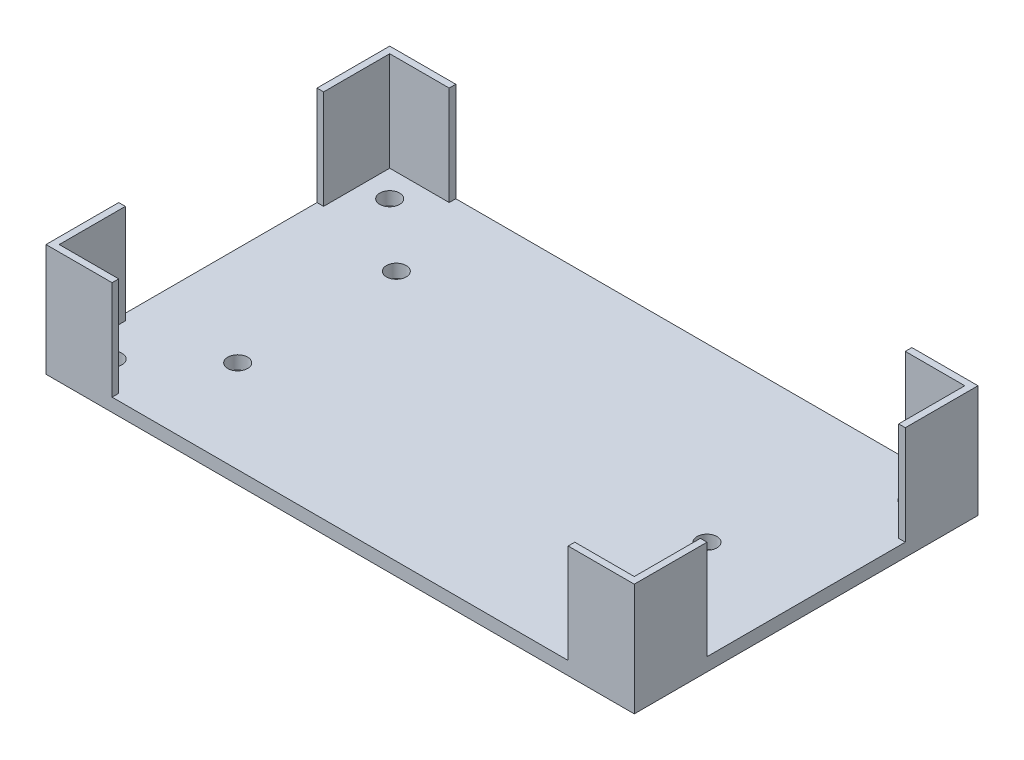
SolidWorks part; units mm, degrees
ref_plane "Front Plane" through (0, 0, 0) normal (0, 0, 1) x (1, 0, 0)
ref_plane "Top Plane" through (0, 0, 0) normal (0, 1, 0) x (1, 0, 0)
ref_plane "Right Plane" through (0, 0, 0) normal (1, 0, 0) x (0, 0, -1)
sketch "Sketch1" plane through (0, 0, 0) normal (0, 1, 0) x (1, 0, 0)
  line L1 (-60.2291, 12.7329) -> (28.7709, 12.7329)
  line L2 (-60.2291, 12.7329) -> (-60.2291, -39.2671)
  line L3 (-60.2291, -39.2671) -> (28.7709, -39.2671)
  line L4 (28.7709, 12.7329) -> (28.7709, -39.2671)
  dimension "D1" = 52
  dimension "D2" = 89
extrude "Boss-Extrude1" add sketch "Sketch1" along normal blind 2 contours L2 L1 L4 L3
sketch "Sketch2" plane through (0, 2, 0) normal (0, 1, 0) x (1, 0, 0)
  line L0 (-60.2291, 12.7329) -> (-60.2291, -39.2671) construction
  line L1 (-60.2291, -39.2671) -> (28.7709, -39.2671) construction
  line L2 (-60.2291, 12.7329) -> (28.7709, 12.7329) construction
  line L3 (28.7709, 12.7329) -> (28.7709, -39.2671) construction
  circle A0 centre (-55.2291, -34.2671) radius 1.5
  circle A1 centre (-55.2291, 7.7329) radius 1.5
  circle A2 centre (23.7709, 7.7329) radius 1.5
  circle A3 centre (23.7709, -34.2671) radius 1.5
  point P16 (0, 0)
  point P17 (0, 0)
  point P18 (0, 0)
  dimension "D1" = 3
  dimension "D4" = 3
  dimension "D7" = 3
  dimension "D8" = 5
  dimension "D12" = 3
  dimension "D2" = 5
  dimension "D3" = 5
  dimension "D5" = 5
  dimension "D6" = 5
  dimension "D9" = 5
  dimension "D10" = 5
  dimension "D11" = 5
extrude "Cut-Extrude1" cut sketch "Sketch2" against normal through all
sketch "Sketch5" plane through (0, 2, 0) normal (0, 1, 0) x (1, 0, 0)
  line L0 (-60.2291, 12.7329) -> (-60.2291, -39.2671) construction
  line L1 (-60.2291, -39.2671) -> (28.7709, -39.2671) construction
  line L3 (28.7709, 12.7329) -> (28.7709, -39.2671) construction
  circle A0 centre (-45.2291, -25.2671) radius 1.5
  circle A1 centre (-45.2291, -1.2671) radius 1.5
  circle A2 centre (13.7709, -13.2671) radius 1.5
  point P10 (0, 0)
  point P11 (0, 0)
  dimension "D1" = 3
  dimension "D2" = 3
  dimension "D3" = 3
  dimension "D4" = 15
  dimension "D5" = 14
  dimension "D6" = 15
  dimension "D7" = 24
  dimension "D8" = 26
  dimension "D9" = 15
extrude "Cut-Extrude3" cut sketch "Sketch5" against normal through all
sketch "Sketch6" plane through (0, 2, 0) normal (0, 1, 0) x (1, 0, 0)
  line L0 (-60.2291, 12.7329) -> (-60.2291, -39.2671) construction
  line L1 (-60.2291, -38.2671) -> (-59.2291, -38.2671)
  line L2 (-60.2291, -38.2671) -> (-60.2291, -28.2671)
  line L3 (-60.2291, -28.2671) -> (-59.2291, -28.2671)
  line L4 (-59.2291, -38.2671) -> (-59.2291, -28.2671)
  line L5 (-60.2291, -39.2671) -> (28.7709, -39.2671) construction
  line L6 (-60.2291, 1.7329) -> (-59.2291, 1.7329)
  line L7 (-60.2291, 1.7329) -> (-60.2291, 11.7329)
  line L8 (-60.2291, 11.7329) -> (-59.2291, 11.7329)
  line L9 (-59.2291, 1.7329) -> (-59.2291, 11.7329)
  line L10 (-60.2291, 12.7329) -> (28.7709, 12.7329) construction
  line L11 (28.7709, 12.7329) -> (28.7709, -39.2671) construction
  line L12 (27.7709, -38.2671) -> (28.7709, -38.2671)
  line L13 (27.7709, -38.2671) -> (27.7709, -28.2671)
  line L14 (27.7709, -28.2671) -> (28.7709, -28.2671)
  line L15 (28.7709, -38.2671) -> (28.7709, -28.2671)
  line L17 (27.7709, 1.7329) -> (28.7709, 1.7329)
  line L18 (27.7709, 1.7329) -> (27.7709, 11.7329)
  line L19 (27.7709, 11.7329) -> (28.7709, 11.7329)
  line L20 (28.7709, 1.7329) -> (28.7709, 11.7329)
  line L21 (-60.2291, -39.2671) -> (-50.2291, -39.2671)
  line L22 (-60.2291, -39.2671) -> (-60.2291, -38.2671)
  line L23 (-60.2291, -38.2671) -> (-50.2291, -38.2671)
  line L24 (-50.2291, -39.2671) -> (-50.2291, -38.2671)
  line L25 (18.7709, -39.2671) -> (28.7709, -39.2671)
  line L26 (18.7709, -39.2671) -> (18.7709, -38.2671)
  line L27 (18.7709, -38.2671) -> (28.7709, -38.2671)
  line L28 (28.7709, -39.2671) -> (28.7709, -38.2671)
  line L29 (-60.2291, 11.7329) -> (-50.2291, 11.7329)
  line L30 (-60.2291, 11.7329) -> (-60.2291, 12.7329)
  line L31 (-60.2291, 12.7329) -> (-50.2291, 12.7329)
  line L32 (-50.2291, 11.7329) -> (-50.2291, 12.7329)
  line L33 (18.7709, 11.7329) -> (28.7709, 11.7329)
  line L34 (18.7709, 11.7329) -> (18.7709, 12.7329)
  line L35 (18.7709, 12.7329) -> (28.7709, 12.7329)
  line L36 (28.7709, 11.7329) -> (28.7709, 12.7329)
  point P20 (28.2709, -38.2671)
  point P41 (28.7709, 12.2329)
  line M33 (28.7709, -39.2671) -> (28.7709, 12.7329)
  line M34 (28.7709, 12.7329) -> (-60.2291, 12.7329)
  line M35 (-60.2291, 12.7329) -> (-60.2291, -39.2671)
  dimension "D1" = 10
  dimension "D2" = 1
  dimension "D3" = 0
  dimension "D4" = 1
  dimension "D5" = 0
  dimension "D6" = 1
  dimension "D7" = 30
  dimension "D8" = 1
  dimension "D9" = 10
  dimension "D10" = 1
  dimension "D11" = 0
  dimension "D12" = 1
  dimension "D13" = 10
  dimension "D14" = 1
  dimension "D15" = 0
  dimension "D16" = 1
  dimension "D17" = 10
  dimension "D18" = 0
  dimension "D19" = 0
  dimension "D20" = 1
  dimension "D21" = 10
  dimension "D22" = 1
  dimension "D23" = 0
  dimension "D24" = 0
  dimension "D25" = 10
  dimension "D26" = 0
  dimension "D27" = 0
  dimension "D28" = 1
  dimension "D29" = 10
  dimension "D30" = 1
  dimension "D31" = 0
  dimension "D32" = 0
extrude "Boss-Extrude3" add sketch "Sketch6" along normal blind 15 contours L1 L4 L3 M35 | L34 L33 L19 M33 M34 | L22 L21 L24 L23 | L7 L8 L9 L6 | L31 L32 L29 L30 | L25 L28 L27 L26 | L13 L14 L15 L12
